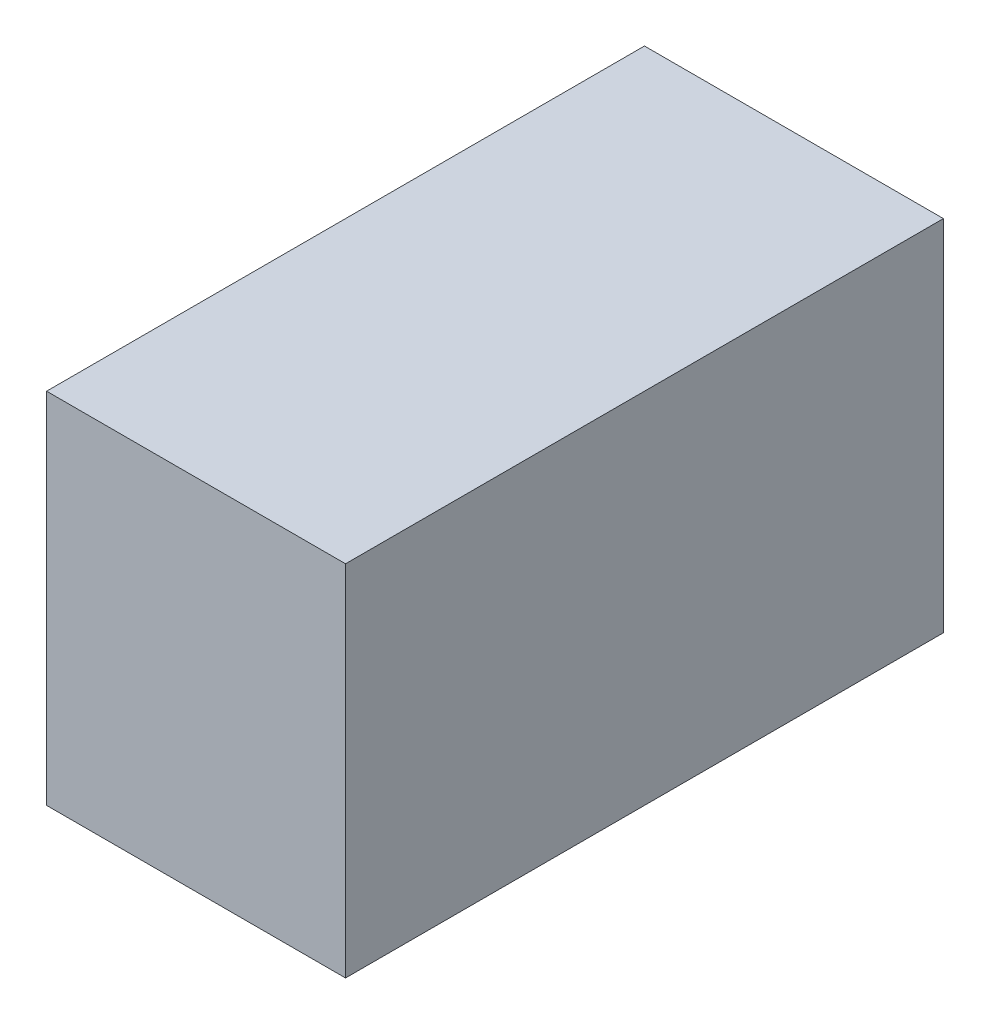
SolidWorks part; units mm, degrees
ref_plane "Front Plane" through (0, 0, 0) normal (0, 0, 1) x (1, 0, 0)
ref_plane "Top Plane" through (0, 0, 0) normal (0, 1, 0) x (1, 0, 0)
ref_plane "Right Plane" through (0, 0, 0) normal (1, 0, 0) x (0, 0, -1)
sketch "Sketch1" plane through (0, 0, 0) normal (1, 0, 0) x (0, 0, -1)
  line L0 (-10.0542, 4.4097) -> (-10.0542, 0.5997)
  line L1 (-10.0542, 0.5997) -> (-3.7042, 0.5997)
  line L2 (-3.7042, 0.5997) -> (-3.7042, 4.4097)
  line L3 (-3.7042, 4.4097) -> (-10.0542, 4.4097)
  dimension "D1" = 6.35
  dimension "D2" = 3.81
extrude "Boss-Extrude1" add sketch "Sketch1" along normal blind 3.175
